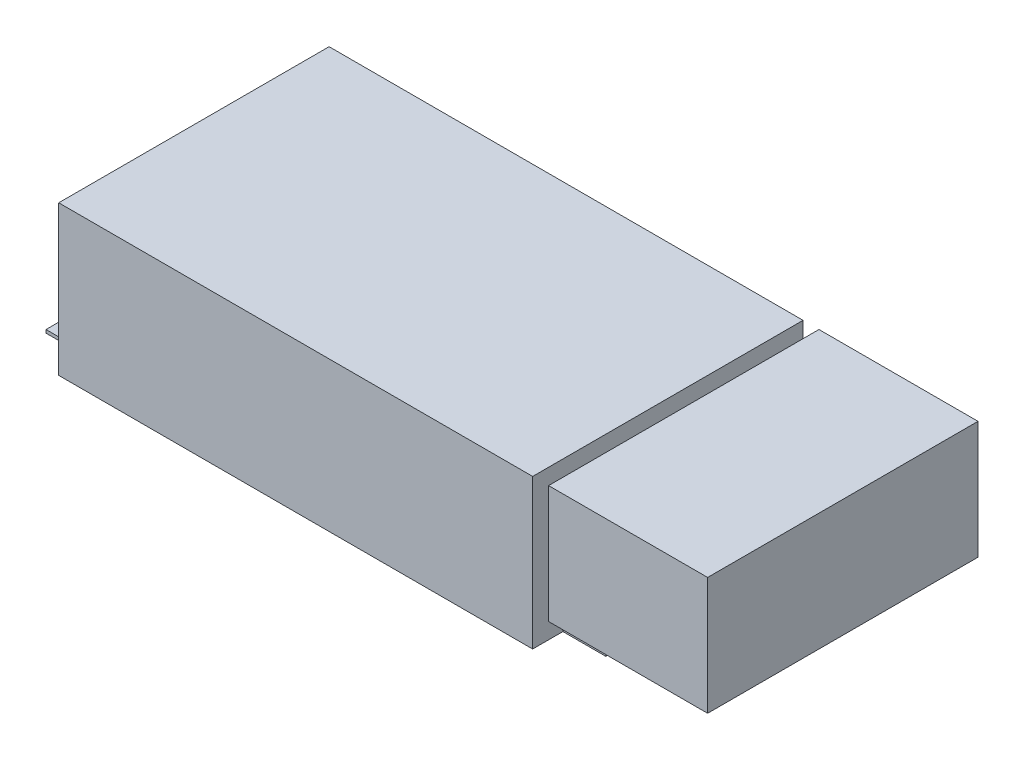
SolidWorks part; units mm, degrees
ref_plane "Спереди" through (0, 0, 0) normal (0, 0, 1) x (1, 0, 0)
ref_plane "Сверху" through (0, 0, 0) normal (0, 1, 0) x (1, 0, 0)
ref_plane "Справа" through (0, 0, 0) normal (1, 0, 0) x (0, 0, -1)
sketch "Эскиз1" plane through (0, 0, 0) normal (0, 1, 0) x (1, 0, 0)
  line L1 (-74.5, -42.5) -> (74.5, -42.5)
  line L2 (-74.5, -42.5) -> (-74.5, 42.5)
  line L3 (-74.5, 42.5) -> (74.5, 42.5)
  line L4 (74.5, -42.5) -> (74.5, 42.5)
  line L5 (-74.5, -42.5) -> (74.5, 42.5) construction
  line L6 (-74.5, 42.5) -> (74.5, -42.5) construction
  point P0 (0, 0)
  dimension "D1" = 85
  dimension "D2" = 149
extrude "Бобышка-Вытянуть1" add sketch "Эскиз1" along normal blind 47
sketch "Эскиз2" plane through (0, 0, 0) normal (0, -1, 0) x (1, 0, 0)
  line L0 (-85, -1000.6143) -> (-85, 48999.3857) construction
  line L1 (-88, -33) -> (88, -33)
  line L2 (-88, -33) -> (-88, 33)
  line L3 (-88, 33) -> (88, 33)
  line L4 (88, -33) -> (88, 33)
  line L5 (-88, -33) -> (88, 33) construction
  line L6 (-88, 33) -> (88, -33) construction
  line L7 (85, -996.1916) -> (85, 49003.8084) construction
  line L8 (-1000, 0) -> (49000, 0) construction
  line L9 (-1010.5652, 27.5) -> (48989.4348, 27.5) construction
  line L10 (-1003.6855, -27.5) -> (48996.3145, -27.5) construction
  line L11 (-81.5, 24) -> (-81.5, 18) construction
  line L12 (-78, 24) -> (-78, 18)
  line L13 (-85, 24) -> (-85, 18)
  line L14 (-81.5, -24) -> (-81.5, -18) construction
  line L15 (-78, -24) -> (-78, -18)
  line L16 (-85, -24) -> (-85, -18)
  line L17 (0, -1000) -> (0, 49000) construction
  line L18 (81.5, 24) -> (81.5, 18) construction
  line L19 (78, 24) -> (78, 18)
  line L20 (85, 24) -> (85, 18)
  line L21 (81.5, -24) -> (81.5, -18) construction
  line L22 (78, -24) -> (78, -18)
  line L23 (85, -24) -> (85, -18)
  circle A0 centre (-81.5, 0) radius 3.5
  circle A1 centre (81.5, 0) radius 3.5
  arc A2 (-78, 24) -> (-85, 24) centre (-81.5, 24) ccw
  arc A3 (-85, 18) -> (-78, 18) centre (-81.5, 18) ccw
  arc A4 (-78, -24) -> (-85, -24) centre (-81.5, -24) cw
  arc A5 (-85, -18) -> (-78, -18) centre (-81.5, -18) cw
  arc A6 (78, 24) -> (85, 24) centre (81.5, 24) cw
  arc A7 (85, 18) -> (78, 18) centre (81.5, 18) cw
  arc A8 (78, -24) -> (85, -24) centre (81.5, -24) ccw
  arc A9 (85, -18) -> (78, -18) centre (81.5, -18) ccw
  point P0 (0, 0)
  point P22 (-81.5, 21)
  point P29 (-81.5, -21)
  point P38 (81.5, 21)
  point P45 (81.5, -21)
  dimension "D5" = 7
  dimension "D8" = 13
  dimension "D1" = 66
  dimension "D2" = 176
  dimension "D3" = 3
  dimension "D4" = 3
  dimension "D6" = 5.5
  dimension "D7" = 5.5
extrude "Бобышка-Вытянуть2" add sketch "Эскиз2" against normal blind 1
sketch "Эскиз3" plane through (74.5, 0, 0) normal (1, 0, 0) x (0, 0, -1)
  line L0 (-42.5, 47) -> (-42.5, 0) construction
  line L1 (42.5, 47) -> (-42.5, 47)
  line L2 (42.5, 47) -> (42.5, 10)
  line L3 (42.5, 10) -> (-42.5, 10)
  line L4 (-42.5, 47) -> (-42.5, 10)
  line L5 (33, 0) -> (42.5, 0) construction
  dimension "D1" = 10
extrude "Бобышка-Вытянуть3" add sketch "Эскиз3" along normal blind 50 from offset 5 separate body
